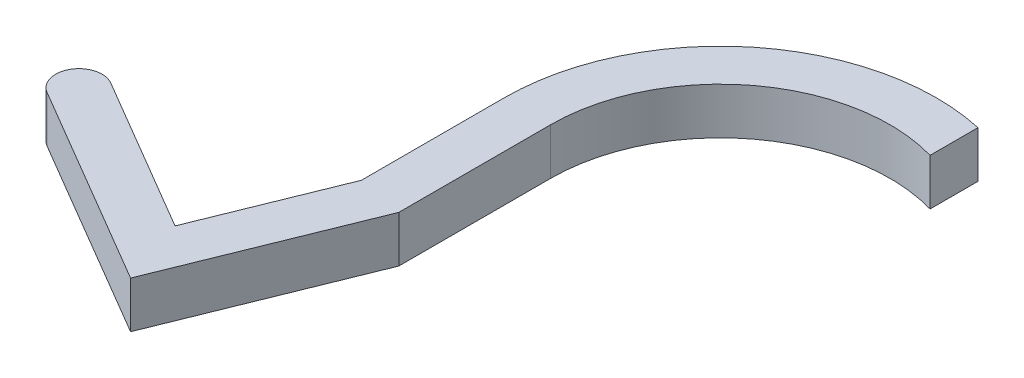
SolidWorks part; units mm, degrees
ref_plane "Plan de face" through (0, 0, 0) normal (0, 0, 1) x (1, 0, 0)
ref_plane "Plan de dessus" through (0, 0, 0) normal (0, 1, 0) x (1, 0, 0)
ref_plane "Plan de droite" through (0, 0, 0) normal (1, 0, 0) x (0, 0, -1)
sketch "Esquisse1" plane through (0, 0, 0) normal (0, 1, 0) x (1, 0, 0)
  line L0 (10, 45.412) -> (10, 35.1034)
  line L1 (-46.5, 0) -> (-36.5, 0)
  circle A0 centre (0, 0) radius 36.5 construction
  circle A2 centre (0, 0) radius 46.5 construction
  arc A3 (-36.5, 0) -> (10, 35.1034) centre (0, 0) cw
  arc A4 (-46.5, 0) -> (10, 45.412) centre (0, 0) cw
  point P0 (0, 0)
  point P11 (0, 0)
  dimension "D1" = 73
  dimension "D2" = 93
  dimension "D3" = 10
extrude "Boss.-Extru.1" add sketch "Esquisse1" along normal blind 10
sketch "Esquisse2" plane through (0, 0, 0) normal (0, 1, 0) x (1, 0, 0)
  line L0 (-94.1769, 60.0165) -> (0, 0) construction
  line L1 (-47.0884, 30.0083) -> (-94.1328, -43.8129) construction
  circle A0 centre (0, 0) radius 36.5 construction
  circle A1 centre (-94.1769, 60.0165) radius 36.5 construction
  circle A2 centre (-94.1328, -43.8129) radius 103.8294 construction
  point P5 (-97.6639, 64.7244)
  point P10 (-107.2402, -55.7712)
  point P11 (-90.8965, -46.028)
  point P12 (-97.3033, 53.4658)
  point P13 (-94.1328, 60.0165)
  dimension "D1" = 73
  dimension "D2" = 73
sketch "Esquisse3" plane through (0, 0, 0) normal (0, 1, 0) x (1, 0, 0)
  line L2 (-68.23, -16.3658) -> (19.7777, -157.8212) construction
  line L3 (19.7777, -157.8212) -> (-164.6068, -157.8212) construction
sketch "Esquisse4" plane through (0, 10, 0) normal (0, 1, 0) x (1, 0, 0)
  line L0 (-46.5, -30.7027) -> (-62.3798, -69.9699) construction
  line L1 (-36.5, 0) -> (-46.5, 0)
  line L2 (-36.5, 0) -> (-36.5, -32.6482)
  line L3 (-36.5, -32.6482) -> (-46.5, -32.6482) construction
  line L4 (-46.5, 0) -> (-46.5, -32.6482) construction
  line L5 (-62.3798, -69.9699) -> (-53.1092, -73.7189) construction
  line L6 (-53.1092, -73.7189) -> (-36.5, -32.6482)
  line L7 (-96.6659, -48.1237) -> (-53.1092, -73.7189)
  line L8 (-53.1092, -73.7189) -> (-48.0428, -65.0973) construction
  line L9 (-48.0428, -65.0973) -> (-91.5996, -39.5021) construction
  line L10 (-46.5, 0) -> (-46.5, -30.7027)
  line L11 (-46.5, -30.7027) -> (-58.0348, -59.2257)
  line L12 (-58.0348, -59.2257) -> (-91.5996, -39.5021)
  circle A0 centre (-94.1328, -43.8129) radius 5 construction
  arc A1 (-91.5996, -39.5021) -> (-96.6659, -48.1237) centre (-94.1328, -43.8129) ccw
  point P10 (-52.5783, -73.4721)
  point P18 (-46.5, -30.3912)
  point P19 (-53.1092, -73.7189)
  dimension "D1" = 10
  dimension "D2" = 10
  dimension "D3" = 10
extrude "Boss.-Extru.2" add sketch "Esquisse4" against normal blind 10
